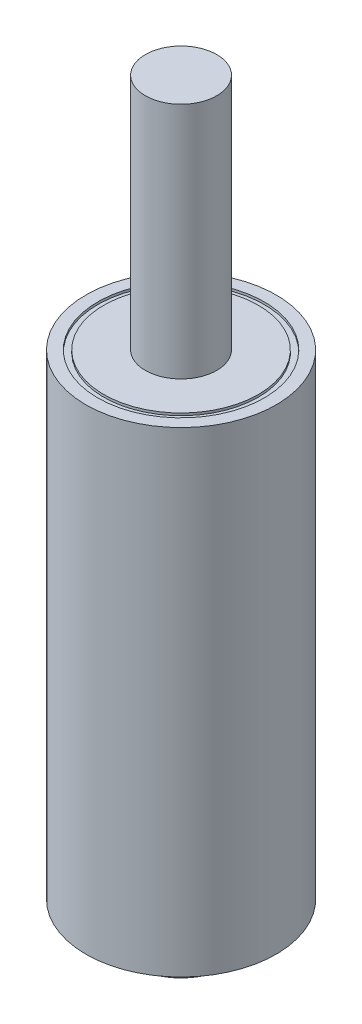
SolidWorks part; units mm, degrees
ref_plane "Front Plane" through (0, 0, 0) normal (0, 0, 1) x (1, 0, 0)
ref_plane "Top Plane" through (0, 0, 0) normal (0, 1, 0) x (1, 0, 0)
ref_plane "Right Plane" through (0, 0, 0) normal (1, 0, 0) x (0, 0, -1)
sketch "Sketch1" plane through (0, 0, 0) normal (0, 1, 0) x (1, 0, 0)
  circle A0 centre (0, 0) radius 4
  dimension "D1" = 8
extrude "Boss-Extrude1" add sketch "Sketch1" along normal blind 20
sketch "Sketch2" plane through (0, 0, 0) normal (0, -1, 0) x (1, 0, 0)
  circle A0 centre (0, 0) radius 3.5
  circle A1 centre (0, 0) radius 4 construction
  dimension "D1" = 0.5
extrude "Cut-Extrude-Thin1" cut sketch "Sketch2" against normal blind 0.1 thin thin type one direction reverse wall 0.25
sketch "Sketch3" plane through (0, 0, 0) normal (0, -1, 0) x (1, 0, 0)
  circle A0 centre (0, 0) radius 2
  dimension "D1" = 4
extrude "Boss-Extrude2" add sketch "Sketch3" along normal blind 0.2
fillet "Fillet1" radius 0.1 1 edges at (0, -0.2, -2)
sketch "Sketch4" plane through (0, -0.2, 0) normal (0, -1, 0) x (1, 0, 0)
  circle A0 centre (0, 0) radius 2
  dimension "D1" = 4
extrude "Boss-Extrude3" add sketch "Sketch4" along normal blind 1
fillet "Fillet2" radius 0.1 1 edges at (0, -1.2, -2)
sketch "Sketch5" plane through (0, -1.2, 0) normal (0, -1, 0) x (1, 0, 0)
  circle A0 centre (0, 0) radius 1.25
  dimension "D1" = 2.5
extrude "Boss-Extrude4" add sketch "Sketch5" along normal blind 0.5
chamfer "Chamfer1" distance 0.2 angle 45 1 edges at (0, -1.7, -1.25)
sketch "Sketch6" plane through (0, -1.2, 0) normal (0, -1, 0) x (1, 0, 0)
  line L0 (0, -1.25) -> (0, -2)
  line L1 (1.25, 0) -> (2, 0)
  arc A0 (2, 0) -> (0, -2) centre (0, 0) ccw
  arc A1 (1.25, 0) -> (0, -1.25) centre (0, 0) ccw
  circle A2 centre (0, 0) radius 2 construction
  circle A3 centre (0, 0) radius 1.25 construction
extrude "Boss-Extrude5" add sketch "Sketch6" along normal blind 0.25
sketch "Sketch7" plane through (0, 20, 0) normal (0, 1, 0) x (1, 0, 0)
  circle A0 centre (0, 0) radius 1.5
  dimension "D1" = 3
extrude "Boss-Extrude6" add sketch "Sketch7" along normal blind 10
sketch "Sketch8" plane through (0, 20, 0) normal (0, 1, 0) x (1, 0, 0)
  circle A0 centre (0, 0) radius 3.5
  circle A1 centre (0, 0) radius 4 construction
  dimension "D1" = 0.5
extrude "Cut-Extrude-Thin2" cut sketch "Sketch8" against normal blind 0.1 thin thin type one direction reverse wall 0.25
